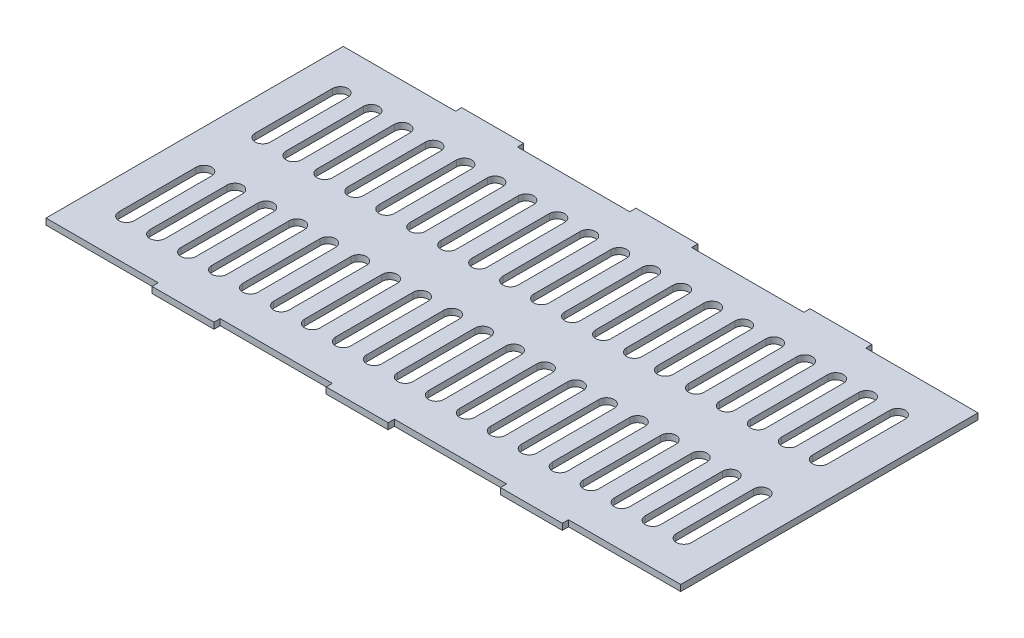
SolidWorks part; units mm, degrees
ref_plane "Front Plane" through (0, 0, 0) normal (0, 0, 1) x (1, 0, 0)
ref_plane "Top Plane" through (0, 0, 0) normal (0, 1, 0) x (1, 0, 0)
ref_plane "Right Plane" through (0, 0, 0) normal (1, 0, 0) x (0, 0, -1)
sketch "Sketch1" plane through (0, 0, 0) normal (0, 1, 0) x (1, 0, 0)
  line L1 (-264.122, 88.09) -> (-19.122, 88.09)
  line L2 (-264.122, 88.09) -> (-264.122, -7.91)
  line L3 (-264.122, -7.91) -> (-19.122, -7.91)
  line L4 (-19.122, 88.09) -> (-19.122, -7.91)
  line L5 (-264.122, 88.09) -> (-19.122, -7.91) construction
  line L6 (-264.122, -7.91) -> (-19.122, 88.09) construction
  point P0 (-141.622, 40.09)
  dimension "D1" = 96
  dimension "D2" = 245
extrude "Boss-Extrude1" add sketch "Sketch1" along normal blind 2 contours L1 L4 L3 L2
sketch "Sketch4" plane through (0, 2, 0) normal (0, 1, 0) x (1, 0, 0)
  line L0 (-264.122, 88.09) -> (-264.122, -7.91) construction
  line L1 (-264.122, -7.91) -> (-264.122, 40.09) construction
  line L2 (-264.122, 40.09) -> (7.3157, 40.09) construction
  line L3 (-264.122, -7.91) -> (-254.122, -7.91) construction
  line L4 (-264.122, -7.91) -> (-19.122, -7.91) construction
  line L5 (-254.122, -7.91) -> (-254.122, 88.09) construction
  line L6 (-264.122, 88.09) -> (-19.122, 88.09) construction
  line L7 (-254.122, -7.91) -> (-249.122, -7.91) construction
  line L8 (-249.122, -7.91) -> (-251.622, -7.91) construction
  line L9 (-251.622, -7.91) -> (-251.622, 88.09) construction
  line L10 (-258.7937, 40.09) -> (-258.7937, 18.09) construction
  line L11 (-258.7937, 18.09) -> (-244.6825, 18.09) construction
  line L12 (-252.8274, 18.09) -> (-252.8274, 5.59) construction
  line L13 (-251.622, 30.59) -> (-251.622, 5.59) construction
  line L14 (-249.1425, 30.59) -> (-249.1425, 5.59)
  line L15 (-254.1016, 30.59) -> (-254.1016, 5.59)
  line L16 (-264.122, -4.1109) -> (-117.122, -4.1109) construction
  line L17 (-244.1016, 30.59) -> (-244.1016, 5.59)
  line L18 (-239.1425, 30.59) -> (-239.1425, 5.59)
  line L19 (-241.622, 30.59) -> (-241.622, 5.59) construction
  line L20 (-234.1016, 30.59) -> (-234.1016, 5.59)
  line L21 (-229.1425, 30.59) -> (-229.1425, 5.59)
  line L22 (-231.622, 30.59) -> (-231.622, 5.59) construction
  line L23 (-224.1016, 30.59) -> (-224.1016, 5.59)
  line L24 (-219.1425, 30.59) -> (-219.1425, 5.59)
  line L25 (-221.622, 30.59) -> (-221.622, 5.59) construction
  line L26 (-214.1016, 30.59) -> (-214.1016, 5.59)
  line L27 (-209.1425, 30.59) -> (-209.1425, 5.59)
  line L28 (-211.622, 30.59) -> (-211.622, 5.59) construction
  line L29 (-204.1016, 30.59) -> (-204.1016, 5.59)
  line L30 (-199.1425, 30.59) -> (-199.1425, 5.59)
  line L31 (-201.622, 30.59) -> (-201.622, 5.59) construction
  line L32 (-194.1016, 30.59) -> (-194.1016, 5.59)
  line L33 (-189.1425, 30.59) -> (-189.1425, 5.59)
  line L34 (-191.622, 30.59) -> (-191.622, 5.59) construction
  line L35 (-184.1016, 30.59) -> (-184.1016, 5.59)
  line L36 (-179.1425, 30.59) -> (-179.1425, 5.59)
  line L37 (-181.622, 30.59) -> (-181.622, 5.59) construction
  line L38 (-174.1016, 30.59) -> (-174.1016, 5.59)
  line L39 (-169.1425, 30.59) -> (-169.1425, 5.59)
  line L40 (-171.622, 30.59) -> (-171.622, 5.59) construction
  line L41 (-164.1016, 30.59) -> (-164.1016, 5.59)
  line L42 (-159.1425, 30.59) -> (-159.1425, 5.59)
  line L43 (-161.622, 30.59) -> (-161.622, 5.59) construction
  line L44 (-154.1016, 30.59) -> (-154.1016, 5.59)
  line L45 (-149.1425, 30.59) -> (-149.1425, 5.59)
  line L46 (-151.622, 30.59) -> (-151.622, 5.59) construction
  line L47 (-144.1016, 30.59) -> (-144.1016, 5.59)
  line L48 (-139.1425, 30.59) -> (-139.1425, 5.59)
  line L49 (-141.622, 30.59) -> (-141.622, 5.59) construction
  line L50 (-134.1016, 30.59) -> (-134.1016, 5.59)
  line L51 (-129.1425, 30.59) -> (-129.1425, 5.59)
  line L52 (-131.622, 30.59) -> (-131.622, 5.59) construction
  line L53 (-124.1016, 30.59) -> (-124.1016, 5.59)
  line L54 (-119.1425, 30.59) -> (-119.1425, 5.59)
  line L55 (-121.622, 30.59) -> (-121.622, 5.59) construction
  line L56 (-121.622, 49.59) -> (-121.622, 74.59) construction
  line L57 (-119.1425, 49.59) -> (-119.1425, 74.59)
  line L58 (-124.1016, 49.59) -> (-124.1016, 74.59)
  line L59 (-131.622, 49.59) -> (-131.622, 74.59) construction
  line L60 (-129.1425, 49.59) -> (-129.1425, 74.59)
  line L61 (-134.1016, 49.59) -> (-134.1016, 74.59)
  line L62 (-141.622, 49.59) -> (-141.622, 74.59) construction
  line L63 (-139.1425, 49.59) -> (-139.1425, 74.59)
  line L64 (-144.1016, 49.59) -> (-144.1016, 74.59)
  line L65 (-151.622, 49.59) -> (-151.622, 74.59) construction
  line L66 (-149.1425, 49.59) -> (-149.1425, 74.59)
  line L67 (-154.1016, 49.59) -> (-154.1016, 74.59)
  line L68 (-161.622, 49.59) -> (-161.622, 74.59) construction
  line L69 (-159.1425, 49.59) -> (-159.1425, 74.59)
  line L70 (-164.1016, 49.59) -> (-164.1016, 74.59)
  line L71 (-171.622, 49.59) -> (-171.622, 74.59) construction
  line L72 (-169.1425, 49.59) -> (-169.1425, 74.59)
  line L73 (-174.1016, 49.59) -> (-174.1016, 74.59)
  line L74 (-181.622, 49.59) -> (-181.622, 74.59) construction
  line L75 (-179.1425, 49.59) -> (-179.1425, 74.59)
  line L76 (-184.1016, 49.59) -> (-184.1016, 74.59)
  line L77 (-191.622, 49.59) -> (-191.622, 74.59) construction
  line L78 (-189.1425, 49.59) -> (-189.1425, 74.59)
  line L79 (-194.1016, 49.59) -> (-194.1016, 74.59)
  line L80 (-201.622, 49.59) -> (-201.622, 74.59) construction
  line L81 (-199.1425, 49.59) -> (-199.1425, 74.59)
  line L82 (-204.1016, 49.59) -> (-204.1016, 74.59)
  line L83 (-211.622, 49.59) -> (-211.622, 74.59) construction
  line L84 (-209.1425, 49.59) -> (-209.1425, 74.59)
  line L85 (-214.1016, 49.59) -> (-214.1016, 74.59)
  line L86 (-221.622, 49.59) -> (-221.622, 74.59) construction
  line L87 (-219.1425, 49.59) -> (-219.1425, 74.59)
  line L88 (-224.1016, 49.59) -> (-224.1016, 74.59)
  line L89 (-231.622, 49.59) -> (-231.622, 74.59) construction
  line L90 (-229.1425, 49.59) -> (-229.1425, 74.59)
  line L91 (-234.1016, 49.59) -> (-234.1016, 74.59)
  line L92 (-241.622, 49.59) -> (-241.622, 74.59) construction
  line L93 (-239.1425, 49.59) -> (-239.1425, 74.59)
  line L94 (-244.1016, 49.59) -> (-244.1016, 74.59)
  line L95 (-251.622, 49.59) -> (-251.622, 74.59) construction
  line L96 (-249.1425, 49.59) -> (-249.1425, 74.59)
  line L97 (-254.1016, 49.59) -> (-254.1016, 74.59)
  line L98 (-111.622, 30.59) -> (-111.622, 5.59) construction
  line L99 (-109.1425, 30.59) -> (-109.1425, 5.59)
  line L100 (-114.1016, 30.59) -> (-114.1016, 5.59)
  line L101 (-101.622, 30.59) -> (-101.622, 5.59) construction
  line L102 (-99.1425, 30.59) -> (-99.1425, 5.59)
  line L103 (-104.1016, 30.59) -> (-104.1016, 5.59)
  line L104 (-91.622, 30.59) -> (-91.622, 5.59) construction
  line L105 (-89.1425, 30.59) -> (-89.1425, 5.59)
  line L106 (-94.1016, 30.59) -> (-94.1016, 5.59)
  line L107 (-81.622, 30.59) -> (-81.622, 5.59) construction
  line L108 (-79.1425, 30.59) -> (-79.1425, 5.59)
  line L109 (-84.1016, 30.59) -> (-84.1016, 5.59)
  line L110 (-71.622, 30.59) -> (-71.622, 5.59) construction
  line L111 (-69.1425, 30.59) -> (-69.1425, 5.59)
  line L112 (-74.1016, 30.59) -> (-74.1016, 5.59)
  line L113 (-71.622, 49.59) -> (-71.622, 74.59) construction
  line L114 (-69.1425, 49.59) -> (-69.1425, 74.59)
  line L115 (-74.1016, 49.59) -> (-74.1016, 74.59)
  line L116 (-81.622, 49.59) -> (-81.622, 74.59) construction
  line L117 (-79.1425, 49.59) -> (-79.1425, 74.59)
  line L118 (-84.1016, 49.59) -> (-84.1016, 74.59)
  line L119 (-91.622, 49.59) -> (-91.622, 74.59) construction
  line L120 (-89.1425, 49.59) -> (-89.1425, 74.59)
  line L121 (-94.1016, 49.59) -> (-94.1016, 74.59)
  line L122 (-101.622, 49.59) -> (-101.622, 74.59) construction
  line L123 (-99.1425, 49.59) -> (-99.1425, 74.59)
  line L124 (-104.1016, 49.59) -> (-104.1016, 74.59)
  line L125 (-111.622, 49.59) -> (-111.622, 74.59) construction
  line L126 (-109.1425, 49.59) -> (-109.1425, 74.59)
  line L127 (-114.1016, 49.59) -> (-114.1016, 74.59)
  line L128 (-69.1425, 12.3278) -> (-59.1425, 12.3278) construction
  line L129 (-59.1425, -7.91) -> (-59.1425, 88.09)
  line L130 (-59.1425, 88.09) -> (-19.122, 88.09)
  line L131 (-19.122, 88.09) -> (-19.122, -7.91)
  line L132 (-19.122, -7.91) -> (-59.1425, -7.91)
  arc A0 (-249.1425, 30.59) -> (-254.1016, 30.59) centre (-251.622, 30.59) ccw
  arc A1 (-254.1016, 5.59) -> (-249.1425, 5.59) centre (-251.622, 5.59) ccw
  arc A2 (-239.1425, 30.59) -> (-244.1016, 30.59) centre (-241.622, 30.59) ccw
  arc A3 (-244.1016, 5.59) -> (-239.1425, 5.59) centre (-241.622, 5.59) ccw
  arc A4 (-229.1425, 30.59) -> (-234.1016, 30.59) centre (-231.622, 30.59) ccw
  arc A5 (-234.1016, 5.59) -> (-229.1425, 5.59) centre (-231.622, 5.59) ccw
  arc A6 (-219.1425, 30.59) -> (-224.1016, 30.59) centre (-221.622, 30.59) ccw
  arc A7 (-224.1016, 5.59) -> (-219.1425, 5.59) centre (-221.622, 5.59) ccw
  arc A8 (-209.1425, 30.59) -> (-214.1016, 30.59) centre (-211.622, 30.59) ccw
  arc A9 (-214.1016, 5.59) -> (-209.1425, 5.59) centre (-211.622, 5.59) ccw
  arc A10 (-199.1425, 30.59) -> (-204.1016, 30.59) centre (-201.622, 30.59) ccw
  arc A11 (-204.1016, 5.59) -> (-199.1425, 5.59) centre (-201.622, 5.59) ccw
  arc A12 (-189.1425, 30.59) -> (-194.1016, 30.59) centre (-191.622, 30.59) ccw
  arc A13 (-194.1016, 5.59) -> (-189.1425, 5.59) centre (-191.622, 5.59) ccw
  arc A14 (-179.1425, 30.59) -> (-184.1016, 30.59) centre (-181.622, 30.59) ccw
  arc A15 (-184.1016, 5.59) -> (-179.1425, 5.59) centre (-181.622, 5.59) ccw
  arc A16 (-169.1425, 30.59) -> (-174.1016, 30.59) centre (-171.622, 30.59) ccw
  arc A17 (-174.1016, 5.59) -> (-169.1425, 5.59) centre (-171.622, 5.59) ccw
  arc A18 (-159.1425, 30.59) -> (-164.1016, 30.59) centre (-161.622, 30.59) ccw
  arc A19 (-164.1016, 5.59) -> (-159.1425, 5.59) centre (-161.622, 5.59) ccw
  arc A20 (-149.1425, 30.59) -> (-154.1016, 30.59) centre (-151.622, 30.59) ccw
  arc A21 (-154.1016, 5.59) -> (-149.1425, 5.59) centre (-151.622, 5.59) ccw
  arc A22 (-139.1425, 30.59) -> (-144.1016, 30.59) centre (-141.622, 30.59) ccw
  arc A23 (-144.1016, 5.59) -> (-139.1425, 5.59) centre (-141.622, 5.59) ccw
  arc A24 (-129.1425, 30.59) -> (-134.1016, 30.59) centre (-131.622, 30.59) ccw
  arc A25 (-134.1016, 5.59) -> (-129.1425, 5.59) centre (-131.622, 5.59) ccw
  arc A26 (-119.1425, 30.59) -> (-124.1016, 30.59) centre (-121.622, 30.59) ccw
  arc A27 (-124.1016, 5.59) -> (-119.1425, 5.59) centre (-121.622, 5.59) ccw
  arc A28 (-119.1425, 49.59) -> (-124.1016, 49.59) centre (-121.622, 49.59) cw
  arc A29 (-124.1016, 74.59) -> (-119.1425, 74.59) centre (-121.622, 74.59) cw
  arc A30 (-129.1425, 49.59) -> (-134.1016, 49.59) centre (-131.622, 49.59) cw
  arc A31 (-134.1016, 74.59) -> (-129.1425, 74.59) centre (-131.622, 74.59) cw
  arc A32 (-139.1425, 49.59) -> (-144.1016, 49.59) centre (-141.622, 49.59) cw
  arc A33 (-144.1016, 74.59) -> (-139.1425, 74.59) centre (-141.622, 74.59) cw
  arc A34 (-149.1425, 49.59) -> (-154.1016, 49.59) centre (-151.622, 49.59) cw
  arc A35 (-154.1016, 74.59) -> (-149.1425, 74.59) centre (-151.622, 74.59) cw
  arc A36 (-159.1425, 49.59) -> (-164.1016, 49.59) centre (-161.622, 49.59) cw
  arc A37 (-164.1016, 74.59) -> (-159.1425, 74.59) centre (-161.622, 74.59) cw
  arc A38 (-169.1425, 49.59) -> (-174.1016, 49.59) centre (-171.622, 49.59) cw
  arc A39 (-174.1016, 74.59) -> (-169.1425, 74.59) centre (-171.622, 74.59) cw
  arc A40 (-179.1425, 49.59) -> (-184.1016, 49.59) centre (-181.622, 49.59) cw
  arc A41 (-184.1016, 74.59) -> (-179.1425, 74.59) centre (-181.622, 74.59) cw
  arc A42 (-189.1425, 49.59) -> (-194.1016, 49.59) centre (-191.622, 49.59) cw
  arc A43 (-194.1016, 74.59) -> (-189.1425, 74.59) centre (-191.622, 74.59) cw
  arc A44 (-199.1425, 49.59) -> (-204.1016, 49.59) centre (-201.622, 49.59) cw
  arc A45 (-204.1016, 74.59) -> (-199.1425, 74.59) centre (-201.622, 74.59) cw
  arc A46 (-209.1425, 49.59) -> (-214.1016, 49.59) centre (-211.622, 49.59) cw
  arc A47 (-214.1016, 74.59) -> (-209.1425, 74.59) centre (-211.622, 74.59) cw
  arc A48 (-219.1425, 49.59) -> (-224.1016, 49.59) centre (-221.622, 49.59) cw
  arc A49 (-224.1016, 74.59) -> (-219.1425, 74.59) centre (-221.622, 74.59) cw
  arc A50 (-229.1425, 49.59) -> (-234.1016, 49.59) centre (-231.622, 49.59) cw
  arc A51 (-234.1016, 74.59) -> (-229.1425, 74.59) centre (-231.622, 74.59) cw
  arc A52 (-239.1425, 49.59) -> (-244.1016, 49.59) centre (-241.622, 49.59) cw
  arc A53 (-244.1016, 74.59) -> (-239.1425, 74.59) centre (-241.622, 74.59) cw
  arc A54 (-249.1425, 49.59) -> (-254.1016, 49.59) centre (-251.622, 49.59) cw
  arc A55 (-254.1016, 74.59) -> (-249.1425, 74.59) centre (-251.622, 74.59) cw
  arc A56 (-109.1425, 30.59) -> (-114.1016, 30.59) centre (-111.622, 30.59) ccw
  arc A57 (-114.1016, 5.59) -> (-109.1425, 5.59) centre (-111.622, 5.59) ccw
  arc A58 (-99.1425, 30.59) -> (-104.1016, 30.59) centre (-101.622, 30.59) ccw
  arc A59 (-104.1016, 5.59) -> (-99.1425, 5.59) centre (-101.622, 5.59) ccw
  arc A60 (-89.1425, 30.59) -> (-94.1016, 30.59) centre (-91.622, 30.59) ccw
  arc A61 (-94.1016, 5.59) -> (-89.1425, 5.59) centre (-91.622, 5.59) ccw
  arc A62 (-79.1425, 30.59) -> (-84.1016, 30.59) centre (-81.622, 30.59) ccw
  arc A63 (-84.1016, 5.59) -> (-79.1425, 5.59) centre (-81.622, 5.59) ccw
  arc A64 (-69.1425, 30.59) -> (-74.1016, 30.59) centre (-71.622, 30.59) ccw
  arc A65 (-74.1016, 5.59) -> (-69.1425, 5.59) centre (-71.622, 5.59) ccw
  arc A66 (-69.1425, 49.59) -> (-74.1016, 49.59) centre (-71.622, 49.59) cw
  arc A67 (-74.1016, 74.59) -> (-69.1425, 74.59) centre (-71.622, 74.59) cw
  arc A68 (-79.1425, 49.59) -> (-84.1016, 49.59) centre (-81.622, 49.59) cw
  arc A69 (-84.1016, 74.59) -> (-79.1425, 74.59) centre (-81.622, 74.59) cw
  arc A70 (-89.1425, 49.59) -> (-94.1016, 49.59) centre (-91.622, 49.59) cw
  arc A71 (-94.1016, 74.59) -> (-89.1425, 74.59) centre (-91.622, 74.59) cw
  arc A72 (-99.1425, 49.59) -> (-104.1016, 49.59) centre (-101.622, 49.59) cw
  arc A73 (-104.1016, 74.59) -> (-99.1425, 74.59) centre (-101.622, 74.59) cw
  arc A74 (-109.1425, 49.59) -> (-114.1016, 49.59) centre (-111.622, 49.59) cw
  arc A75 (-114.1016, 74.59) -> (-109.1425, 74.59) centre (-111.622, 74.59) cw
  point P22 (-251.622, 18.09)
  point P33 (-241.622, 18.09)
  point P40 (-231.622, 18.09)
  point P47 (-221.622, 18.09)
  point P54 (-211.622, 18.09)
  point P61 (-201.622, 18.09)
  point P68 (-191.622, 18.09)
  point P75 (-181.622, 18.09)
  point P82 (-171.622, 18.09)
  point P89 (-161.622, 18.09)
  point P96 (-151.622, 18.09)
  point P103 (-141.622, 18.09)
  point P110 (-131.622, 18.09)
  point P117 (-121.622, 18.09)
  point P122 (-121.622, 62.09)
  point P129 (-131.622, 62.09)
  point P136 (-141.622, 62.09)
  point P143 (-151.622, 62.09)
  point P150 (-161.622, 62.09)
  point P157 (-171.622, 62.09)
  point P164 (-181.622, 62.09)
  point P171 (-191.622, 62.09)
  point P178 (-201.622, 62.09)
  point P185 (-211.622, 62.09)
  point P192 (-221.622, 62.09)
  point P199 (-231.622, 62.09)
  point P206 (-241.622, 62.09)
  point P213 (-251.622, 62.09)
  point P221 (-111.622, 18.09)
  point P228 (-101.622, 18.09)
  point P235 (-91.622, 18.09)
  point P242 (-81.622, 18.09)
  point P249 (-71.622, 18.09)
  point P255 (-71.622, 62.09)
  point P262 (-81.622, 62.09)
  point P269 (-91.622, 62.09)
  point P276 (-101.622, 62.09)
  point P283 (-111.622, 62.09)
  dimension "D1" = 10
  dimension "D2" = 5
  dimension "D3" = 22
  dimension "D4" = 12.5
  dimension "D5" = 147
  dimension "D8" = 10
  dimension "D6" = 14
  dimension "D7" = 6
extrude "Cut-Extrude2" cut sketch "Sketch4" against normal blind 10
sketch "Sketch6" plane through (0, 2, 0) normal (0, 1, 0) x (1, 0, 0)
  line L0 (-264.122, -7.91) -> (-59.1425, -7.91) construction
  line L1 (-59.1425, -7.91) -> (-161.6322, -7.91) construction
sketch "Sketch7" plane through (0, 0, 7.91) normal (0, 0, 1) x (1, 0, 0)
  line L0 (-161.625, 2) -> (-161.6322, 0) construction
  line L1 (-59.1425, 2) -> (-161.6322, 2) construction
  line L2 (-264.122, 0) -> (-59.1425, 0) construction
  line L3 (-161.6286, 1) -> (-171.6286, 1) construction
  line L4 (-161.6286, 1) -> (-151.6289, 0.9279) construction
  line L5 (-171.6286, 2) -> (-171.6286, 1)
  line L7 (-171.6286, 1) -> (-171.6286, 0)
  line L8 (-171.6286, 0) -> (-151.6289, 0)
  line L9 (-151.6289, 0) -> (-151.6289, 2)
  line L10 (-151.6289, 2) -> (-171.6286, 2)
  line L11 (-151.6289, 0.9279) -> (-59.1425, 1) construction
  line L12 (-59.1425, 0) -> (-59.1425, 2) construction
  line L13 (-59.1425, 1) -> (-105.3857, 0.964) construction
  line L14 (-105.3857, 0.964) -> (-105.3857, 1.482) construction
  line L15 (-95.3857, 1.284) -> (-115.3857, 1.284) construction
  line L16 (-115.3857, 2) -> (-115.3857, 0)
  line L17 (-264.122, 2) -> (-59.1425, 2) construction
  line L18 (-115.3857, 0) -> (-95.3857, 0)
  line L19 (-95.3857, 0) -> (-95.3857, 2)
  line L20 (-95.3857, 2) -> (-115.3857, 2)
  line L21 (-264.122, 1) -> (-171.6286, 1) construction
  line L22 (-264.122, 2) -> (-264.122, 0) construction
  line L23 (-217.8753, 1) -> (-217.8753, 1.482) construction
  line L24 (-207.8753, 1.3627) -> (-227.8753, 1.3627) construction
  line L25 (-227.8753, 2) -> (-227.8753, 0)
  line L26 (-227.8753, 0) -> (-207.8753, 0)
  line L27 (-207.8753, 0) -> (-207.8753, 2)
  line L28 (-207.8753, 2) -> (-227.8753, 2)
  point P21 (-105.3857, 1.284)
  point P35 (-217.8753, 1.3627)
  dimension "D1" = 10
  dimension "D2" = 10
  dimension "D3" = 10
extrude "Boss-Extrude2" add sketch "Sketch7" along normal blind 2
sketch "Sketch9" plane through (0, 0, -88.09) normal (0, 0, -1) x (-1, 0, 0)
  point P12 (161.6322, 0.6593)
sketch "Sketch10" plane through (0, 0, -88.09) normal (0, 0, -1) x (-1, 0, 0)
  line L0 (59.1425, 1) -> (264.122, 1) construction
  line L1 (59.1425, 0) -> (59.1425, 2) construction
  line L2 (264.122, 2) -> (264.122, 0) construction
  line L3 (264.122, 1) -> (161.6322, 1) construction
  line L4 (161.6322, 1) -> (161.6322, 2.4257) construction
  line L5 (95.3857, 2) -> (115.3857, 2) construction
  line L6 (115.3857, 2) -> (115.3857, 0) construction
  line L7 (115.3857, 0) -> (95.3857, 0) construction
  line L8 (95.3857, 0) -> (95.3857, 2) construction
  line L9 (171.6286, 2) -> (171.6286, 0) construction
  line L10 (171.6286, 0) -> (151.6289, 0) construction
  line L11 (151.6289, 0) -> (151.6289, 2) construction
  line L12 (151.6289, 2) -> (171.6286, 2) construction
  line L13 (207.8753, 2) -> (227.8753, 2) construction
  line L14 (227.8753, 2) -> (227.8753, 0) construction
  line L15 (227.8753, 0) -> (207.8753, 0) construction
  line L16 (207.8753, 0) -> (207.8753, 2) construction
  line L17 (95.3857, 2) -> (115.3857, 2)
  line L18 (115.3857, 2) -> (115.3857, 0)
  line L19 (115.3857, 0) -> (95.3857, 0)
  line L20 (95.3857, 0) -> (95.3857, 2)
  line L21 (171.6286, 2) -> (171.6286, 0)
  line L22 (171.6286, 0) -> (151.6289, 0)
  line L23 (151.6289, 0) -> (151.6289, 2)
  line L24 (151.6289, 2) -> (171.6286, 2)
  line L25 (207.8753, 2) -> (227.8753, 2)
  line L26 (227.8753, 2) -> (227.8753, 0)
  line L27 (227.8753, 0) -> (207.8753, 0)
  line L28 (207.8753, 0) -> (207.8753, 2)
extrude "Boss-Extrude4" add sketch "Sketch10" along normal blind 2
